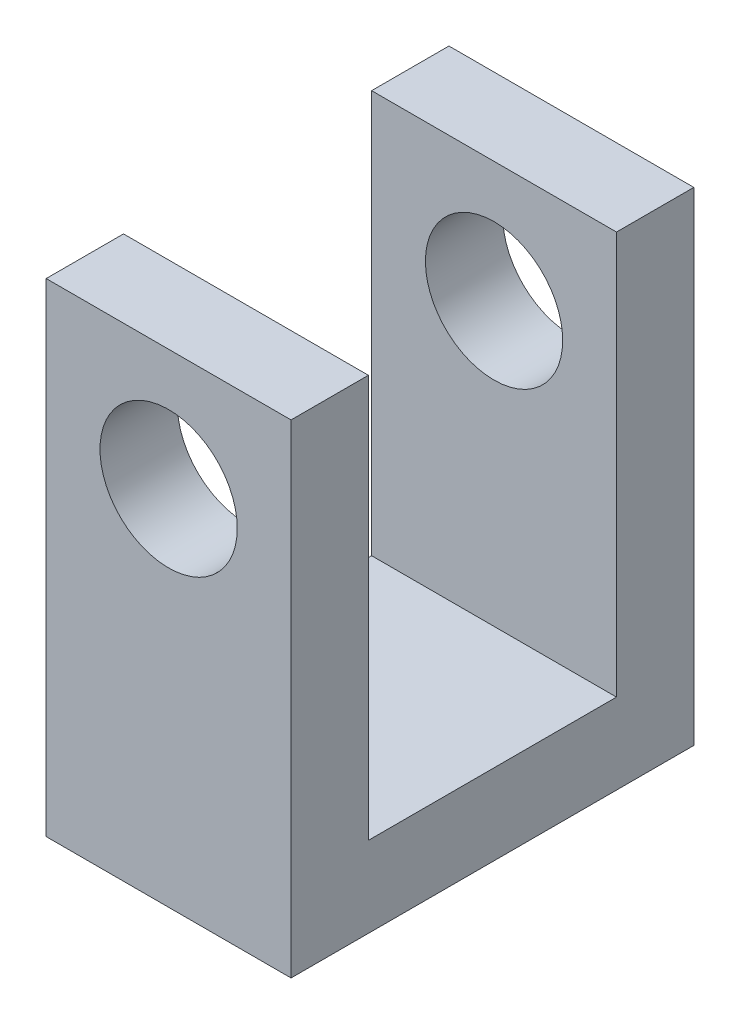
SolidWorks part; units mm, degrees
material "Delrin 2700 NC010, Low Viscosity Acetal Copolymer (SS)"
ref_plane "Front Plane" through (0, 0, 0) normal (0, 0, 1) x (1, 0, 0)
ref_plane "Top Plane" through (0, 0, 0) normal (0, 1, 0) x (1, 0, 0)
ref_plane "Right Plane" through (0, 0, 0) normal (1, 0, 0) x (0, 0, -1)
sketch "Sketch1" plane through (0, 0, 0) normal (0, 1, 0) x (1, 0, 0)
  line L1 (2.413, -3.9688) -> (-2.413, -3.9688)
  line L2 (2.413, -3.9688) -> (2.413, 3.9687)
  line L3 (2.413, 3.9687) -> (-2.413, 3.9687)
  line L4 (-2.413, -3.9688) -> (-2.413, 3.9687)
  line L5 (2.413, -3.9688) -> (-2.413, 3.9687) construction
  line L6 (2.413, 3.9687) -> (-2.413, -3.9688) construction
  point P0 (0, 0)
  dimension "D1" = 7.9375
  dimension "D2" = 4.826
extrude "Boss-Extrude1" add sketch "Sketch1" along normal blind 9.525
sketch "Sketch2" plane through (0, 9.525, 0) normal (0, 1, 0) x (1, 0, 0)
  line L0 (-2.413, 3.9687) -> (-2.413, -3.9688) construction
  line L1 (2.413, 2.4448) -> (-2.413, 2.4448)
  line L2 (2.413, 2.4448) -> (2.413, -2.4448)
  line L3 (2.413, -2.4448) -> (-2.413, -2.4448)
  line L4 (-2.413, 2.4448) -> (-2.413, -2.4448)
  line L5 (2.413, 2.4448) -> (-2.413, -2.4448) construction
  line L6 (2.413, -2.4448) -> (-2.413, 2.4448) construction
  line L7 (-2.413, -3.9688) -> (2.413, -3.9688) construction
  point P0 (0, 0)
  dimension "D1" = 1.524
extrude "Cut-Extrude1" cut sketch "Sketch2" against normal blind 7.9375
hole_wizard "#6-32 Tapped Hole1" positions "Sketch4" profile "Sketch3" tap size "#6-32" standard "ANSI Inch"
sketch "Sketch4" plane through (0, 0, 3.9688) normal (0, 0, 1) x (1, 0, 0)
  line L0 (-2.413, 9.525) -> (2.413, 9.525) construction
  point P0 (0, 7.1438)
  point P5 (0, 9.525)
  dimension "D1" = 2.3813
sketch "Sketch3" plane through (0, 7.1438, 3.9688) normal (1, 0, 0) x (0, -1, 0)
  line L0 (0, 0) -> (0, 9.398)
  line L1 (0, 9.398) -> (1.3525, 9.398)
  line L2 (1.3525, 9.398) -> (1.3525, 0)
  line L5 (1.3525, 0) -> (0, 0)
  line L10 (0, 9.398) -> (-1.3525, 9.398) construction
  line L11 (0, -6.35) -> (0, 107.95) construction
  dimension "Tap Drill Dia." = 2.7051
  dimension "Tap Drill Depth" = 9.398
  dimension "Drill Angle" = 180
cosmetic thread "Hole Thread1" parameters "D1"=7.112, "D2"=3.5052
